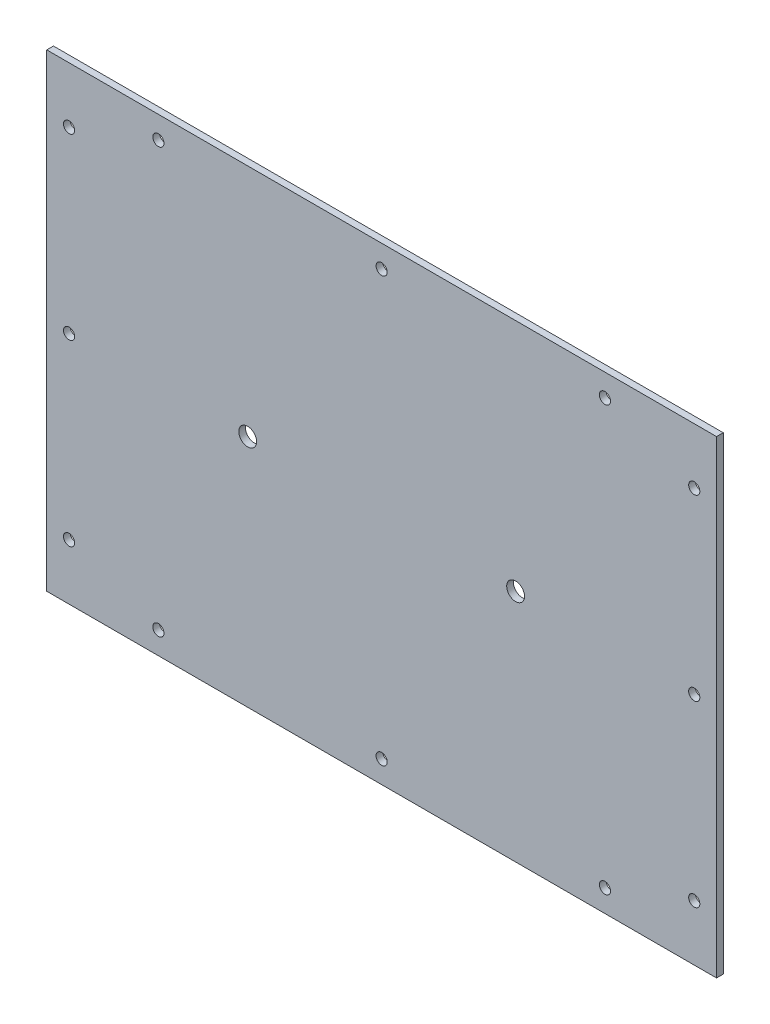
SolidWorks part; units mm, degrees
ref_plane "Alzado" through (0, 0, 0) normal (0, 0, 1) x (1, 0, 0)
ref_plane "Planta" through (0, 0, 0) normal (0, 1, 0) x (1, 0, 0)
ref_plane "Vista lateral" through (0, 0, 0) normal (1, 0, 0) x (0, 0, -1)
sketch "Croquis1" plane through (0, 0, 0) normal (0, 0, 1) x (1, 0, 0)
  line L1 (-150, 105) -> (150, 105)
  line L2 (-150, 105) -> (-150, -105)
  line L3 (-150, -105) -> (150, -105)
  line L4 (150, 105) -> (150, -105)
  line L5 (-150, 105) -> (150, -105) construction
  line L6 (-150, -105) -> (150, 105) construction
  point P0 (0, 0)
  dimension "D1" = 210
  dimension "D2" = 300
extrude "Saliente-Extruir1" add sketch "Croquis1" along normal blind 3
sketch "Croquis3" plane through (0, 0, 3) normal (0, 0, 1) x (1, 0, 0)
  line L0 (0, 105) -> (0, -105) construction
  line L1 (150, 105) -> (-150, 105) construction
  line L2 (-150, -105) -> (150, -105) construction
  line L3 (150, 0) -> (-150, 0) construction
  line L4 (150, -105) -> (150, 105) construction
  line L5 (-150, 105) -> (-150, -105) construction
  circle A0 centre (0, 95) radius 2.5
  circle A3 centre (-140, 0) radius 2.5
  circle A4 centre (100, 95) radius 2.5
  circle A5 centre (-100, 95) radius 2.5
  circle A6 centre (-140, 80) radius 2.5
  circle A7 centre (-140, -80) radius 2.5
  circle A8 centre (100, -95) radius 2.5
  circle A9 centre (-100, -95) radius 2.5
  circle A10 centre (0, -95) radius 2.5
  circle A11 centre (140, -80) radius 2.5
  circle A12 centre (140, 80) radius 2.5
  circle A13 centre (140, 0) radius 2.5
  point P21 (0, 0)
  dimension "D1" = 5
  dimension "D2" = 10
  dimension "D3" = 10
  dimension "D6" = 2
  dimension "D7" = 2
  dimension "D8" = 2
  dimension "D9" = 2
extrude "Cortar-Extruir1" cut sketch "Croquis3" against normal through all
sketch "Croquis4" plane through (0, 0, 3) normal (0, 0, 1) x (1, 0, 0)
  line L0 (-60, 0) -> (60, 0)
  circle A0 centre (-60, 0) radius 4
  circle A1 centre (60, 0) radius 4
  point P4 (0, 0)
  dimension "D2" = 8
  dimension "D1" = 120
extrude "Cortar-Extruir2" cut sketch "Croquis4" against normal through all
